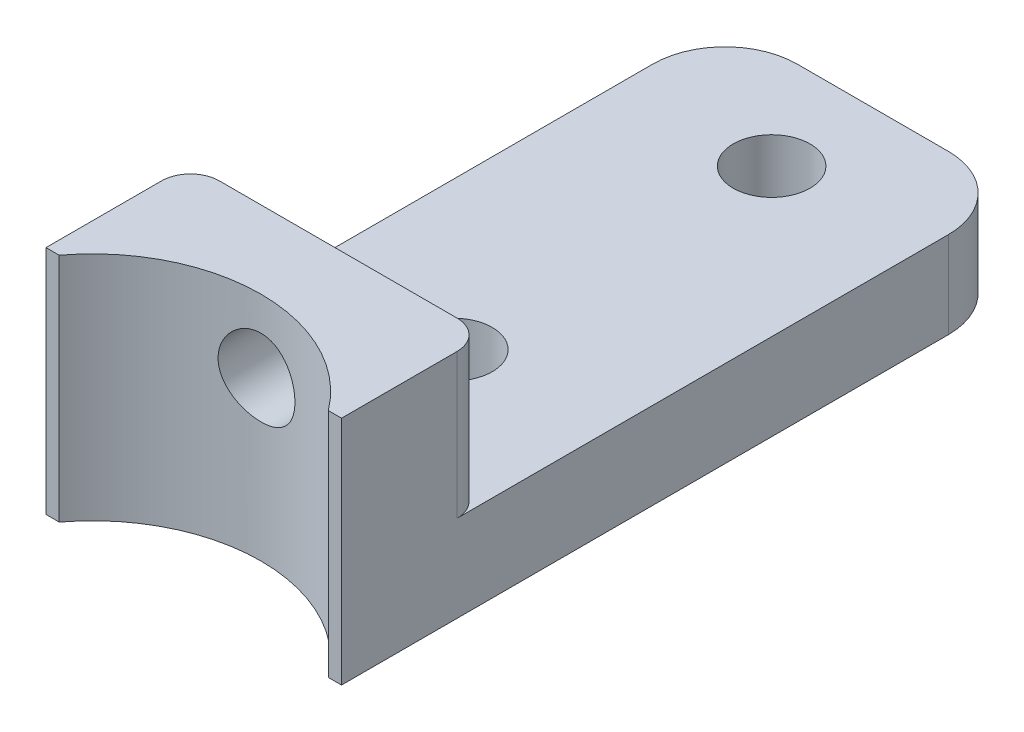
SolidWorks part; units mm, degrees
ref_plane "Front Plane" through (0, 0, 0) normal (0, 0, 1) x (1, 0, 0)
ref_plane "Top Plane" through (0, 0, 0) normal (0, 1, 0) x (1, 0, 0)
ref_plane "Right Plane" through (0, 0, 0) normal (1, 0, 0) x (0, 0, -1)
sketch "Sketch1" plane through (0, 0, 0) normal (0, 1, 0) x (1, 0, 0)
  line L1 (0, 0) -> (25.9783, 0)
  line L2 (0, 0) -> (0, 59.69)
  line L3 (0, 59.69) -> (25.9783, 59.69)
  line L4 (25.9783, 0) -> (25.9783, 59.69)
  dimension "D1" = 59.69
extrude "Boss-Extrude1" add sketch "Sketch1" along normal blind 7.62
sketch "Sketch2" plane through (0, 7.62, 0) normal (0, 1, 0) x (1, 0, 0)
  line L0 (25.9783, 0) -> (25.9783, 59.69) construction
  line L1 (0, 0) -> (25.9783, 0)
  line L2 (0, 0) -> (0, 12.7)
  line L3 (0, 12.7) -> (25.9783, 12.7)
  line L4 (25.9783, 0) -> (25.9783, 12.7)
  dimension "D1" = 12.7
extrude "Boss-Extrude2" add sketch "Sketch2" along normal blind 12.7
sketch "Sketch4" plane through (0, 20.32, 0) normal (0, 1, 0) x (1, 0, 0)
  line L0 (25.9783, 12.7) -> (0, 12.7) construction
  line L1 (0, 0) -> (25.9783, 0) construction
  circle A0 centre (12.9891, -8.89) radius 14.7955
  point P4 (12.9891, 12.7)
  dimension "D1" = 29.591
  dimension "D2" = 8.89
extrude "Cut-Extrude1" cut sketch "Sketch4" against normal up to surface (20.32 mm away) up to face at (12.9891, 0, -29.845)
sketch "Sketch5" plane through (0, 7.62, 0) normal (0, 1, 0) x (1, 0, 0)
  line L0 (12.9891, 59.69) -> (12.9891, 50.8) construction
  line L1 (25.9783, 59.69) -> (0, 59.69) construction
  line L2 (12.9891, 22.86) -> (12.9891, 12.7) construction
  line L3 (25.9783, 12.7) -> (0, 12.7) construction
  point P0 (12.9891, 50.8)
  point P1 (12.9891, 22.86)
  dimension "D1" = 27.94
  dimension "D2" = 10.16
hole_wizard "1/4 Clearance Hole1" positions "Sketch5" profile "Sketch6" hole size "1/4" standard "ANSI Inch" end condition up to next
sketch "Sketch6" plane through (12.9891, 7.62, -50.8) normal (1, 0, 0) x (0, 0, 1)
  line L0 (0, 0) -> (0, 7.62)
  line L1 (0, 7.62) -> (3.3782, 7.62)
  line L2 (3.3782, 7.62) -> (3.3782, 0)
  line L5 (3.3782, 0) -> (0, 0)
  line L11 (0, -6.35) -> (0, 107.95) construction
  dimension "Thru Hole Dia." = 6.7564
  dimension "Thru Hole Depth" = 7.62
fillet "Fillet1" radius 6.35 2 edges at (25.9783, 3.81, -59.69) (0, 3.81, -59.69)
fillet "Fillet2" radius 2.54 2 edges at (25.9783, 13.97, -12.7) (0, 13.97, -12.7)
sketch "Sketch7" plane through (0, 0, -12.7) normal (0, 0, -1) x (-1, 0, 0)
  line L0 (-23.4383, 20.32) -> (-2.54, 20.32) construction
  line L1 (-2.54, 7.62) -> (-2.54, 20.32) construction
  point P0 (-12.9891, 13.97)
  point P3 (-12.9891, 20.32)
  point P6 (-2.54, 13.97)
hole_wizard "1/4 Clearance Hole2" positions "Sketch7" profile "Sketch8" hole size "1/4" standard "ANSI Inch"
sketch "Sketch8" plane through (12.9891, 13.97, -12.7) normal (1, 0, 0) x (0, 1, 0)
  line L0 (0, 0) -> (0, 6.7945)
  line L1 (0, 6.7945) -> (3.3782, 6.7945)
  line L2 (3.3782, 6.7945) -> (3.3782, 0)
  line L5 (3.3782, 0) -> (0, 0)
  line L11 (0, -6.35) -> (0, 107.95) construction
  dimension "Thru Hole Dia." = 6.7564
  dimension "Thru Hole Depth" = 6.7945
